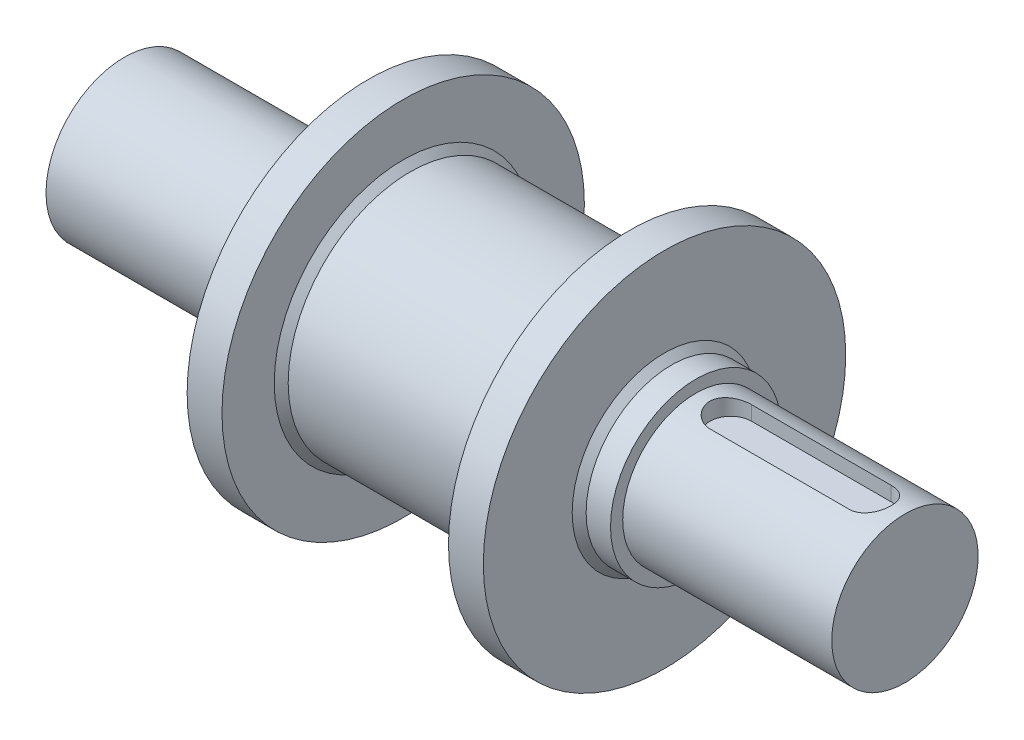
SolidWorks part; units mm, degrees
ref_plane "Front Plane" through (0, 0, 0) normal (0, 0, 1) x (1, 0, 0)
ref_plane "Top Plane" through (0, 0, 0) normal (0, 1, 0) x (1, 0, 0)
ref_plane "Right Plane" through (0, 0, 0) normal (1, 0, 0) x (0, 0, -1)
sketch "Sketch1" plane through (0, 0, 0) normal (0, 0, 1) x (1, 0, 0)
  line L0 (0, 0) -> (0, 22.5)
  line L1 (0, 22.5) -> (65, 22.5)
  line L2 (65, 22.5) -> (65, 27)
  line L3 (65, 27) -> (70, 27)
  line L4 (70, 27) -> (70, 52)
  line L5 (70, 52) -> (80, 52)
  line L6 (80, 52) -> (80, 35)
  line L7 (80, 35) -> (145, 35)
  line L8 (145, 35) -> (145, 52)
  line L9 (145, 52) -> (155, 52)
  line L10 (155, 52) -> (155, 24.5)
  line L11 (155, 24.5) -> (164, 24.5)
  line L14 (164, 24.5) -> (164, 21)
  line L15 (164, 21) -> (224, 21)
  line L16 (224, 21) -> (224, 0)
  line L17 (0, 0) -> (224, 0)
  dimension "D1" = 65
  dimension "D2" = 70
  dimension "D3" = 80
  dimension "D4" = 145
  dimension "D5" = 155
  dimension "D6" = 164
  dimension "D7" = 224
  dimension "D8" = 21
  dimension "D9" = 24.5
  dimension "D10" = 52
  dimension "D11" = 52
  dimension "D12" = 35
  dimension "D13" = 27
  dimension "D14" = 22.5
revolve "Revolve1" add sketch "Sketch1" angle 360 about L17
chamfer "Chamfer1" distance 2 angle 45 3 edges at (155, 0, 24.5) (145, 0, 35) (80, 0, 35)
ref_plane "Plane1" through (0, 21, 0) normal (0, 1, 0) x (1, 0, 0)
sketch "Sketch2" plane through (0, 21, 0) normal (0, 1, 0) x (1, 0, 0)
  line L0 (194, 6) -> (194, -6)
  line L1 (194, -6) -> (174, -6)
  line L2 (194, 6) -> (174, 6)
  line L5 (164, -24.5) -> (164, 24.5) construction
  line L6 (224, 21) -> (164, 21) construction
  arc A0 (174, 6) -> (174, -6) centre (174, 0) ccw
  dimension "D2" = 6
  dimension "D1" = 20
  dimension "D3" = 10
  dimension "D4" = 21
extrude "Cut-Extrude1" cut sketch "Sketch2" against normal blind 5
mirror "Mirror1" about plane through (194, 16, -6) normal (1, 0, 0) of "Cut-Extrude1"
ref_plane "Plane2" through (112.5, 0, 0) normal (1, 0, 0) x (0, 0, -1)
